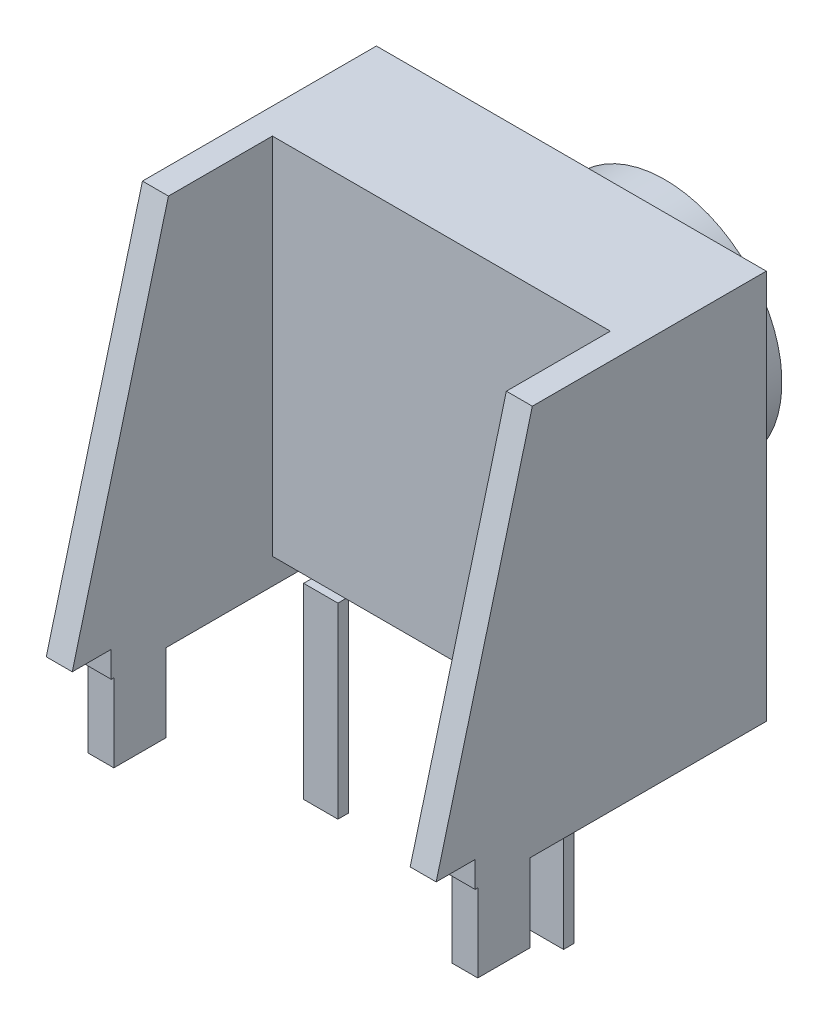
SolidWorks part; units mm, degrees
ref_plane "前视基准面" through (0, 0, 0) normal (0, 0, 1) x (1, 0, 0)
ref_plane "上视基准面" through (0, 0, 0) normal (0, 1, 0) x (1, 0, 0)
ref_plane "右视基准面" through (0, 0, 0) normal (1, 0, 0) x (0, 0, -1)
sketch "草图1" plane through (0, 0, 0) normal (0, 0, 1) x (1, 0, 0)
  line L1 (3.75, -3.5) -> (-3.75, -3.5)
  line L2 (3.75, -3.5) -> (3.75, 3.5)
  line L3 (3.75, 3.5) -> (-3.75, 3.5)
  line L4 (-3.75, -3.5) -> (-3.75, 3.5)
  line L5 (3.75, -3.5) -> (-3.75, 3.5) construction
  line L6 (3.75, 3.5) -> (-3.75, -3.5) construction
  point P0 (0, 0)
extrude "凸台-拉伸1" add sketch "草图1" along normal blind 2.5
sketch "草图2" plane through (0, 0, 0) normal (0, 0, -1) x (-1, 0, 0)
  circle A0 centre (0, 0) radius 2.25
extrude "凸台-拉伸2" add sketch "草图2" along normal blind 1.8
sketch "草图3" plane through (3.75, 0, 0) normal (1, 0, 0) x (0, 0, -1)
  line L0 (0, 3.5) -> (0, -3.5)
  line L1 (0, -3.5) -> (-2.5, -3.5)
  line L2 (-2.5, -3.5) -> (-6.35, -3.5)
  line L3 (-6.35, -3.5) -> (-4.5, 3.5)
  line L4 (-4.5, 3.5) -> (0, 3.5)
extrude "凸台-拉伸3" add sketch "草图3" against normal blind 0.5
sketch "草图4" plane through (3.75, 0, 0) normal (1, 0, 0) x (0, 0, -1)
  line L0 (0, -3.5) -> (-5.05, -3.5) construction
  line L1 (-6.35, -3.5) -> (0, -3.5) construction
  line L2 (-4.55, -3.5) -> (-5.55, -3.5)
  line L3 (-4.55, -3.5) -> (-4.55, -5.5)
  line L4 (-4.55, -5.5) -> (-5.55, -5.5)
  line L5 (-5.55, -5.5) -> (-5.55, -3.5)
  point P8 (-5.05, -3.5)
extrude "凸台-拉伸4" add sketch "草图4" against normal blind 0.5
mirror "镜向1" about plane through (0, 0, 0) normal (1, 0, 0) of "凸台-拉伸4", "凸台-拉伸3"
sketch "草图5" plane through (0, -3.5, 0) normal (0, -1, 0) x (1, 0, 0)
  line L0 (0, 0) -> (0, 2.55) construction
  line L1 (-2.25, 0) -> (2.25, 0) construction
  line L2 (0, 2.55) -> (-2.1697, 2.55) construction
  line L3 (1.8397, 2.65) -> (2.4997, 2.45) construction
  line L4 (-1.8397, 2.45) -> (-2.4997, 2.45)
  line L5 (-1.8397, 2.45) -> (-1.8397, 2.65)
  line L6 (-1.8397, 2.65) -> (-2.4997, 2.65)
  line L7 (-2.4997, 2.45) -> (-2.4997, 2.65)
  line L8 (-1.8397, 2.45) -> (-2.4997, 2.65) construction
  line L9 (-1.8397, 2.65) -> (-2.4997, 2.45) construction
  line L10 (1.8397, 2.45) -> (2.4997, 2.65) construction
  line L11 (2.4997, 2.45) -> (2.4997, 2.65)
  line L12 (1.8397, 2.65) -> (2.4997, 2.65)
  line L13 (1.8397, 2.45) -> (1.8397, 2.65)
  line L14 (1.8397, 2.45) -> (2.4997, 2.45)
  point P9 (0, 0)
extrude "凸台-拉伸5" add sketch "草图5" along normal blind 3.6
sketch "草图6" plane through (0, 0, 0) normal (0, 0, -1) x (-1, 0, 0)
  line L0 (0, 0) -> (0, -4) construction
  line L1 (-3.25, -5.5) -> (-3.25, -3.5) construction
  line L2 (-3.75, -3.5) -> (-3.25, -3.5)
  line L3 (-3.75, -3.5) -> (-3.75, -4)
  line L4 (-3.75, -4) -> (-3.25, -4)
  line L5 (-3.25, -3.5) -> (-3.25, -4)
  line L6 (3.75, -5.5) -> (3.75, -3.5) construction
  line L7 (3.25, -3.5) -> (3.75, -3.5)
  line L8 (3.25, -3.5) -> (3.25, -4)
  line L9 (3.25, -4) -> (3.75, -4)
  line L10 (3.75, -3.5) -> (3.75, -4)
extrude "凸台-拉伸6" add sketch "草图6" against normal blind 5.6
